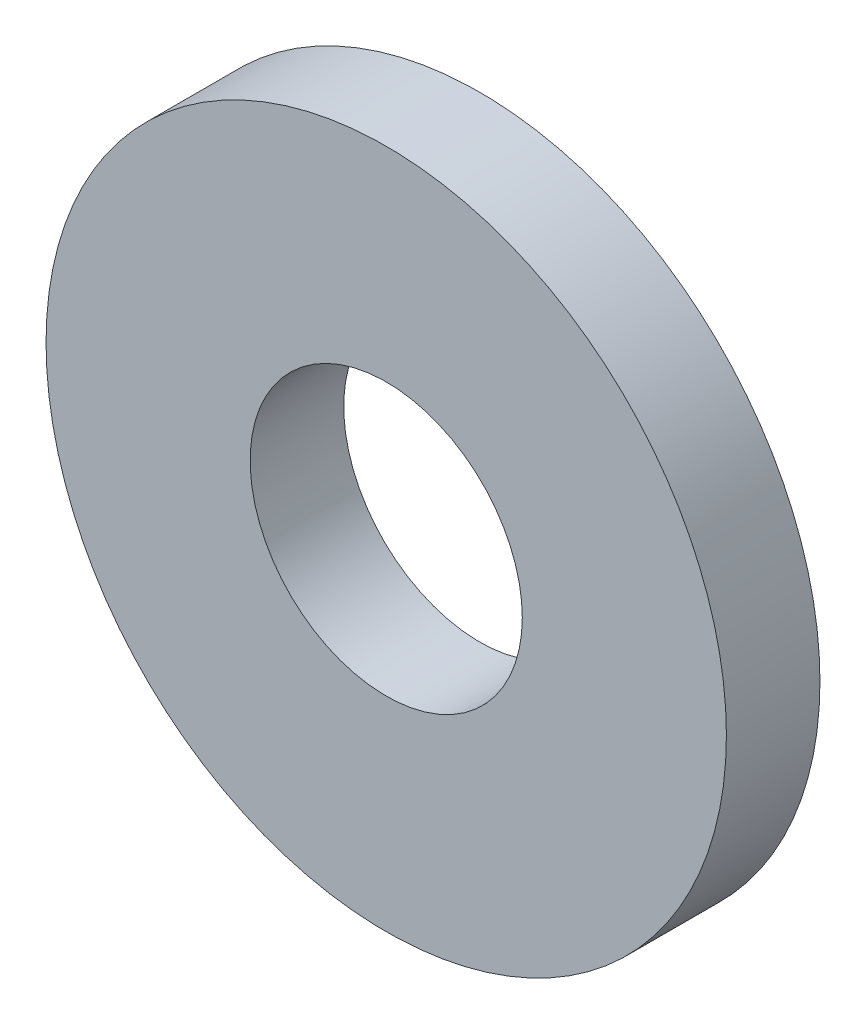
SolidWorks part; units mm, degrees
ref_plane "Front Plane" through (0, 0, 0) normal (0, 0, 1) x (1, 0, 0)
ref_plane "Top Plane" through (0, 0, 0) normal (0, 1, 0) x (1, 0, 0)
ref_plane "Right Plane" through (0, 0, 0) normal (1, 0, 0) x (0, 0, -1)
sketch "Sketch1" plane through (0, 0, 0) normal (0, 0, 1) x (1, 0, 0)
  circle A0 centre (0, 0) radius 4
  circle A1 centre (0, 0) radius 1.6
  dimension "OD" = 8
  dimension "ID1" = 3.2
extrude "Boss-Extrude1" add sketch "Sketch1" along normal blind 1.1
